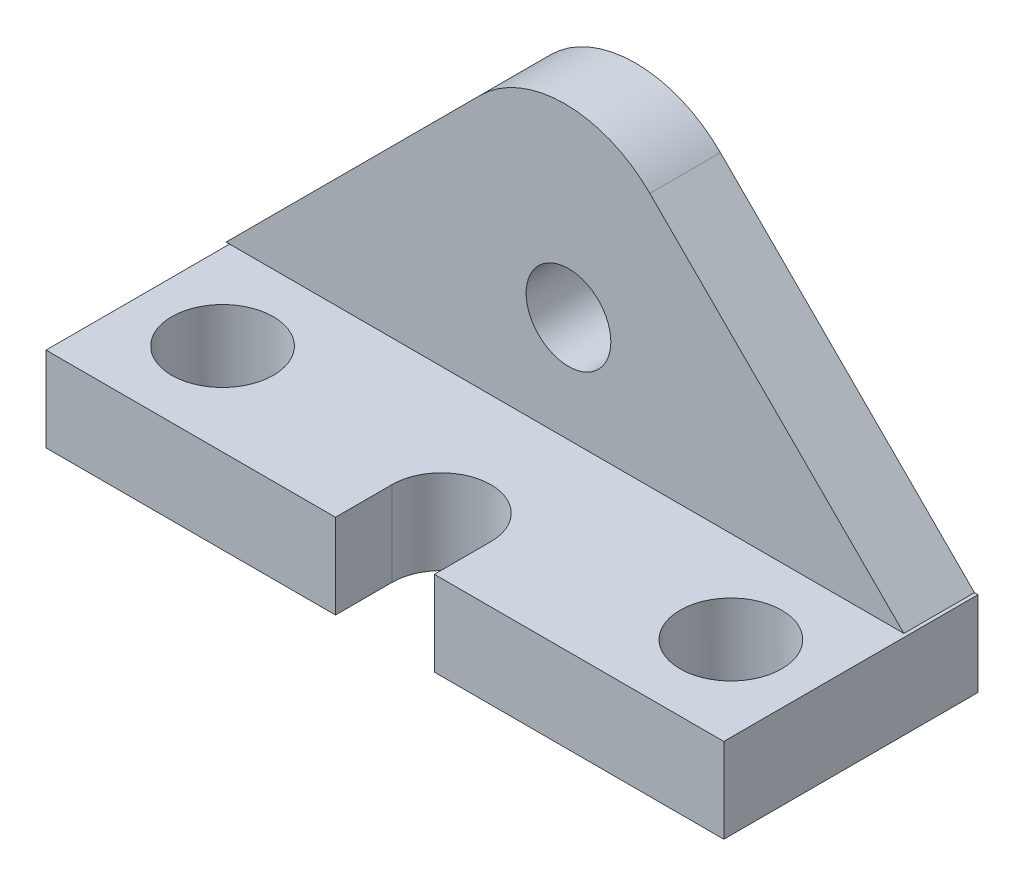
SolidWorks part; units mm, degrees
ref_plane "Front Plane" through (0, 0, 0) normal (0, 0, 1) x (1, 0, 0)
ref_plane "Top Plane" through (0, 0, 0) normal (0, 1, 0) x (1, 0, 0)
ref_plane "Right Plane" through (0, 0, 0) normal (1, 0, 0) x (0, 0, -1)
sketch "Sketch1" plane through (0, 0, 0) normal (0, 0, 1) x (1, 0, 0)
  line L0 (-48.4974, 0) -> (47.5026, 0)
  line L2 (0, 15) -> (0, 32) construction
  line L4 (47.5026, 0) -> (11.5234, 35.9792)
  line L5 (-48.4974, 0) -> (-12.5182, 35.9792)
  circle A0 centre (0, 15) radius 6
  arc A1 (-12.5182, 35.9792) -> (11.5234, 35.9792) centre (-0.4974, 23.9584) cw
  dimension "D3" = 12
  dimension "D2" = 17
  dimension "D1" = 96
  dimension "D4" = 17
extrude "Boss-Extrude2" add sketch "Sketch1" along normal mid plane 10
sketch "Sketch2" plane through (0, 0, 0) normal (1, 0, 0) x (0, 0, -1)
  line L1 (5, 0) -> (-31, 0)
  line L2 (5, 0) -> (5, -12)
  line L3 (5, -12) -> (-31, -12)
  line L4 (-31, 0) -> (-31, -12)
  dimension "D1" = 12
  dimension "D2" = 36
extrude "Boss-Extrude3" add sketch "Sketch2" along normal mid plane 96
sketch "Sketch3" plane through (0, 0, 0) normal (0, 1, 0) x (1, 0, 0)
  line L0 (-48, -31) -> (0, -31) construction
  line L1 (48, -31) -> (-48, -31) construction
  line L2 (0, -31) -> (0, -16) construction
  line L7 (-7, -23) -> (-7, -31)
  line L8 (-7, -31) -> (7, -31)
  line L9 (7, -31) -> (7, -23)
  arc A1 (0, -16) -> (-7, -23) centre (0, -23) ccw
  arc A2 (0, -16) -> (7, -23) centre (0, -23) cw
  dimension "D2" = 7
  dimension "D1" = 15
extrude "Cut-Extrude1" cut sketch "Sketch3" against normal mid plane 96
sketch "Sketch4" plane through (0, 0, 0) normal (0, 1, 0) x (1, 0, 0)
  line L0 (-48, -31) -> (-36, -31) construction
  line L1 (-7, -31) -> (-48, -31) construction
  line L2 (-36, -31) -> (-36, -5) construction
  line L3 (-48, -5) -> (47.5026, -5) construction
  circle A0 centre (-36, -18) radius 7.2
  dimension "D2" = 14.4
  dimension "D1" = 12
extrude "Cut-Extrude2" cut sketch "Sketch4" against normal mid plane 96
sketch "Sketch5" plane through (0, 0, 0) normal (0, 1, 0) x (1, 0, 0)
  line L0 (48, -31) -> (36, -31) construction
  line L1 (48, -31) -> (7, -31) construction
  line L2 (36, -31) -> (36, -5) construction
  line L3 (47.5026, -5) -> (11.5234, -5) construction
  circle A0 centre (36, -18) radius 7.2
  dimension "D2" = 14.4
  dimension "D1" = 12
extrude "Cut-Extrude3" cut sketch "Sketch5" against normal mid plane 96
